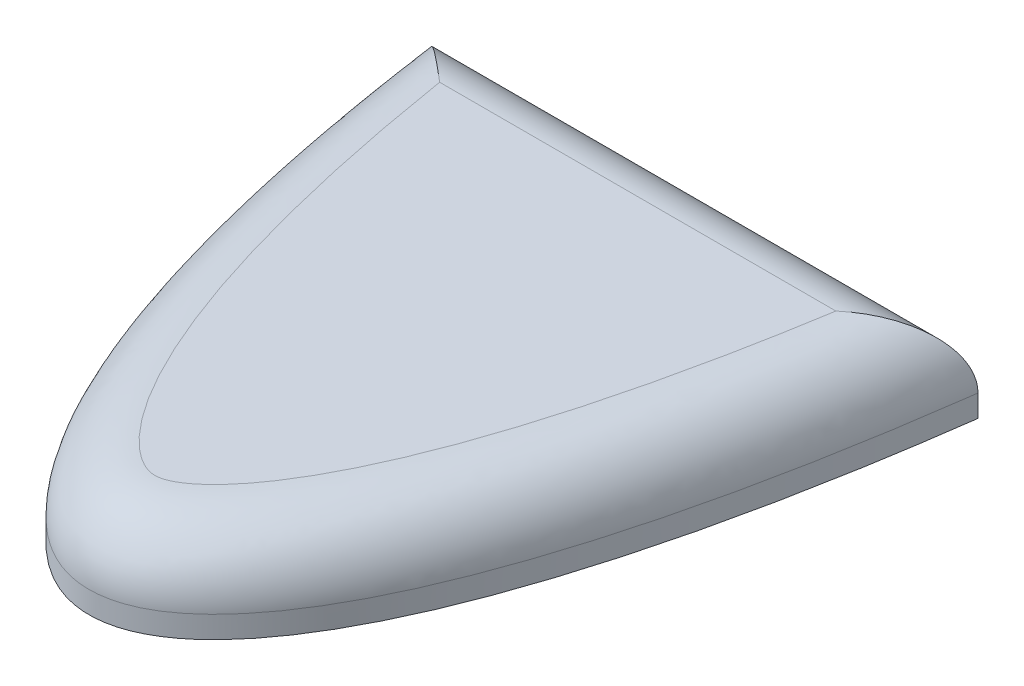
SolidWorks part; units mm, degrees
material "Nylon 6/10"
ref_plane "Front Plane" through (0, 0, 0) normal (0, 0, 1) x (1, 0, 0)
ref_plane "Top Plane" through (0, 0, 0) normal (0, 1, 0) x (1, 0, 0)
ref_plane "Right Plane" through (0, 0, 0) normal (1, 0, 0) x (0, 0, -1)
sketch "Sketch1" plane through (0, 0, 0) normal (0, 1, 0) x (1, 0, 0)
  line L0 (0, 0) -> (0, 9.4638) construction
  line L1 (-12.5, 9.4638) -> (12.5, 9.4638)
  spline S0 degree 3 poles (12.5, 9.4638) (7.5, -27.8695) (-7.5, -27.8695) (-12.5, 9.4638) knots 0 0 0 0 1 1 1 1
  point P6 (0, 9.4638)
  dimension "D1" = 28
  dimension "D2" = 30
  dimension "D3" = 25
extrude "Boss-Extrude1" add sketch "Sketch1" along normal blind 4
fillet "Fillet1" radius 3 2 edges at (0, 4, -9.4638)
sketch "Sketch2" plane through (0, 0, 0) normal (0, -1, 0) x (1, 0, 0)
  line L0 (12.5, -9.4638) -> (-12.5, -9.4638) construction
  circle A0 centre (0, 6.5362) radius 1.75
  dimension "D2" = 3.5
  dimension "D1" = 16
extrude "Boss-Extrude2" add sketch "Sketch2" along normal blind 2
sketch "Sketch3" plane through (0, -2, 0) normal (0, -1, 0) x (1, 0, 0)
  circle A0 centre (0, 6.5362) radius 2
  dimension "D1" = 4
extrude "Boss-Extrude3" add sketch "Sketch3" along normal blind 1 from offset 1
